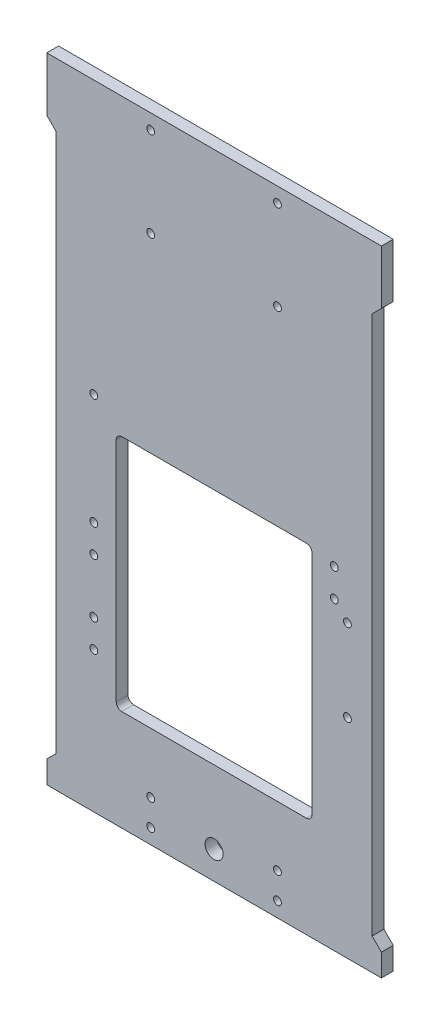
SolidWorks part; units mm, degrees
material "Maple"
ref_plane "Front Plane" through (0, 0, 0) normal (0, 0, 1) x (1, 0, 0)
ref_plane "Top Plane" through (0, 0, 0) normal (0, 1, 0) x (1, 0, 0)
ref_plane "Right Plane" through (0, 0, 0) normal (1, 0, 0) x (0, 0, -1)
sketch "Sketch1" plane through (0, 0, 0) normal (0, 0, 1) x (1, 0, 0)
  line L0 (-89.75, 0) -> (89.75, 0)
  line L1 (-89.75, 0) -> (-89.75, 12)
  line L2 (-89.75, 12) -> (-84.75, 17)
  line L3 (-84.75, 17) -> (-84.75, 306)
  line L4 (0, 0) -> (0, 48.9324) construction
  line L5 (89.75, 0) -> (89.75, 12)
  line L6 (89.75, 12) -> (84.75, 17)
  line L7 (84.75, 17) -> (84.75, 306)
  line L8 (-84.75, 306) -> (-89.75, 311)
  line L9 (-89.75, 311) -> (-89.75, 340)
  line L10 (-89.75, 340) -> (89.75, 340)
  line L11 (89.75, 340) -> (89.75, 311)
  line L12 (89.75, 311) -> (84.75, 306)
  dimension "D1" = 45
  dimension "D2" = 179.5
  dimension "D3" = 5
  dimension "D4" = 340
  dimension "D5" = 12
  dimension "D6" = 29
extrude "Boss-Extrude1" add sketch "Sketch1" along normal blind 6.35
sketch "Sketch2" plane through (0, 0, 6.35) normal (0, 0, 1) x (1, 0, 0)
  line L1 (-49.5, 181.8665) -> (49.5, 181.8665)
  line L2 (-52.5, 178.8665) -> (-52.5, 57.1322)
  line L3 (-49.5, 54.1322) -> (49.5, 54.1322)
  line L4 (52.5, 178.8665) -> (52.5, 57.1322)
  line L32 (39, 74.1322) -> (29.5, 74.1322) construction
  line L35 (-49, 179.8665) -> (-39.5, 179.8665) construction
  arc A0 (49.5, 54.1322) -> (52.5, 57.1322) centre (49.5, 57.1322) ccw
  arc A1 (49.5, 181.8665) -> (52.5, 178.8665) centre (49.5, 178.8665) cw
  arc A2 (-52.5, 57.1322) -> (-49.5, 54.1322) centre (-49.5, 57.1322) ccw
  arc A3 (-49.5, 181.8665) -> (-52.5, 178.8665) centre (-49.5, 178.8665) ccw
  point P18 (0, 54.1322)
  point P22 (52.5, 54.1322)
  point P27 (-52.5, 54.1322)
  point P30 (-52.5, 181.8665)
  point P31 (45, 82.9994)
  dimension "D5" = 3
  dimension "D2" = 2
  dimension "D4" = 105
  dimension "D1" = 20
extrude "Cut-Extrude1" cut sketch "Sketch2" against normal through all
sketch "Sketch3" plane through (0, 0, 6.35) normal (0, 0, 1) x (1, 0, 0)
  circle A0 centre (-64.5, 75.4994) radius 2.1
  circle A1 centre (-64.5, 90.4994) radius 2.1
  circle A2 centre (-64.5, 134.4994) radius 2.1
  circle A3 centre (-64.5, 119.4994) radius 2.1
  circle A4 centre (-64.5, 193.9052) radius 2.1
  circle A5 centre (64.5, 163.4994) radius 2.1
  circle A6 centre (64.5, 178.4994) radius 2.1
  circle A7 centre (71.5016, 155.8535) radius 2.1
  circle A8 centre (71.5016, 111.8535) radius 2.1
  circle A15 centre (64.5, 178.4994) radius 3.2375 construction
  circle A16 centre (64.5, 163.4994) radius 3.2375 construction
  circle A17 centre (-64.5, 193.9052) radius 1.85 construction
  dimension "D1" = 4.2
extrude "Cut-Extrude2" cut sketch "Sketch3" against normal through all
sketch "Sketch4" plane through (0, 0, 6.35) normal (0, 0, 1) x (1, 0, 0)
  circle A0 centre (-34, 332) radius 2.1
  circle A1 centre (34, 332) radius 2.1
  circle A2 centre (34, 284) radius 2.1
  circle A3 centre (-34, 284) radius 2.1
  circle A4 centre (-34, 8) radius 2.1
  circle A5 centre (-34, 22.001) radius 2.1
  circle A6 centre (34, 22.001) radius 2.1
  circle A7 centre (34, 8) radius 2.1
  dimension "D1" = 4.2
  dimension "D2" = 4.2
extrude "Cut-Extrude3" cut sketch "Sketch4" against normal through all
sketch "Sketch5" plane through (0, 0, 6.35) normal (0, 0, 1) x (1, 0, 0)
  circle A0 centre (0, 15.0005) radius 4.85
  circle A1 centre (0, 15.0005) radius 4.85 construction
extrude "Cut-Extrude4" cut sketch "Sketch5" against normal through all
